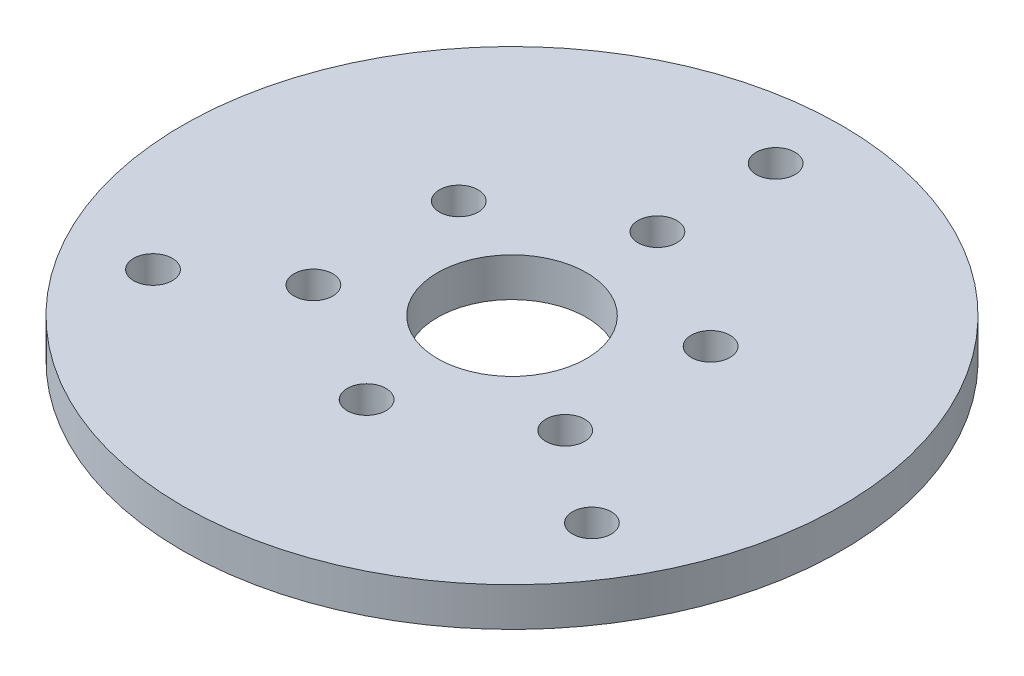
SolidWorks part; units mm, degrees
ref_plane "Front Plane" through (0, 0, 0) normal (0, 0, 1) x (1, 0, 0)
ref_plane "Top Plane" through (0, 0, 0) normal (0, 1, 0) x (1, 0, 0)
ref_plane "Right Plane" through (0, 0, 0) normal (1, 0, 0) x (0, 0, -1)
sketch "Sketch1" plane through (0, 0, 0) normal (0, 1, 0) x (1, 0, 0)
  line L0 (-35.941, -22.86) -> (35.941, -22.86) construction
  line L1 (35.941, -22.86) -> (0, -22.86) construction
  line L2 (0, -22.86) -> (0, 0) construction
  circle A0 centre (0, 0) radius 53.975
  circle A1 centre (0, 43.18) radius 3.175
  circle A2 centre (35.941, -22.86) radius 3.175
  circle A3 centre (-35.941, -22.86) radius 3.175
  dimension "D1" = 71.882
  dimension "D4" = 107.95
  dimension "D5" = 6.35
  dimension "D2" = 66.04
  dimension "D3" = 22.86
extrude "Boss-Extrude1" add sketch "Sketch1" along normal blind 6.35
sketch "Sketch2" plane through (0, 6.35, 0) normal (0, 1, 0) x (1, 0, 0)
  circle A0 centre (0, 0) radius 23.8125 construction
  circle A1 centre (0, 23.8125) radius 3.175
  circle A2 centre (20.6222, 11.9063) radius 3.175
  circle A3 centre (20.6222, -11.9062) radius 3.175
  circle A4 centre (0, -23.8125) radius 3.175
  circle A5 centre (-20.6222, -11.9063) radius 3.175
  circle A6 centre (-20.6222, 11.9062) radius 3.175
  circle A7 centre (0, 0) radius 12.2
  point P17 (0, 0)
  dimension "D1" = 6.35
  dimension "D3" = 47.625
  dimension "D4" = 24.4
  dimension "D2" = 6
extrude "Cut-Extrude1" cut sketch "Sketch2" against normal through all
